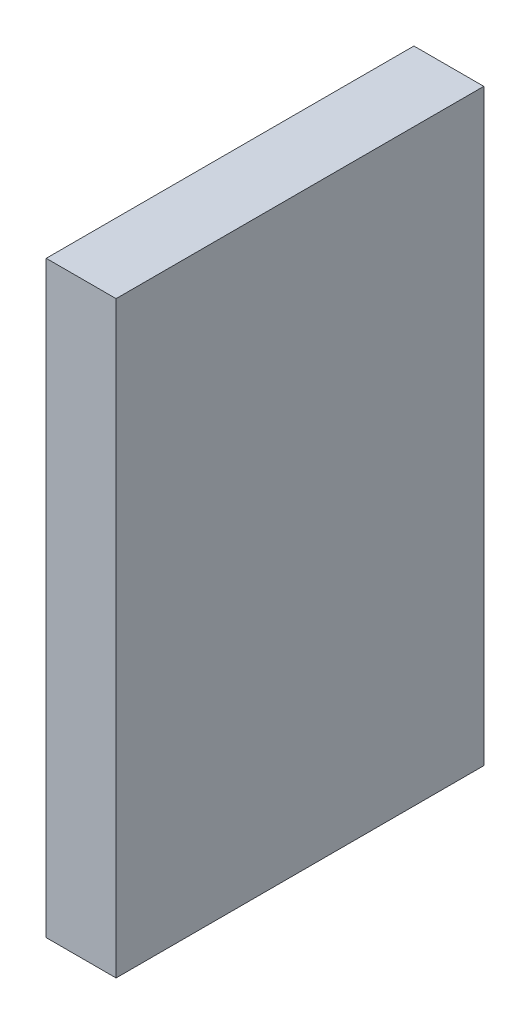
SolidWorks part; units mm, degrees
ref_plane "Front Plane" through (0, 0, 0) normal (0, 0, 1) x (1, 0, 0)
ref_plane "Top Plane" through (0, 0, 0) normal (0, 1, 0) x (1, 0, 0)
ref_plane "Right Plane" through (0, 0, 0) normal (1, 0, 0) x (0, 0, -1)
sketch "Sketch1" plane through (0, 0, 0) normal (1, 0, 0) x (0, 0, -1)
  line L1 (-25, -40) -> (25, -40)
  line L2 (-25, -40) -> (-25, 40)
  line L3 (-25, 40) -> (25, 40)
  line L4 (25, -40) -> (25, 40)
  line L5 (-25, -40) -> (25, 40) construction
  line L6 (-25, 40) -> (25, -40) construction
  point P0 (0, 0)
  dimension "D1" = 50
  dimension "D2" = 80
extrude "Boss-Extrude1" add sketch "Sketch1" along normal blind 9.5
